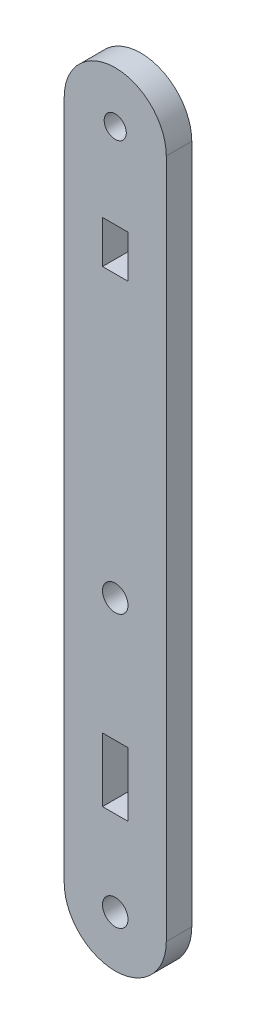
SolidWorks part; units mm, degrees
ref_plane "Front Plane" through (0, 0, 0) normal (0, 0, 1) x (1, 0, 0)
ref_plane "Top Plane" through (0, 0, 0) normal (0, 1, 0) x (1, 0, 0)
ref_plane "Right Plane" through (0, 0, 0) normal (1, 0, 0) x (0, 0, -1)
sketch "Model" plane through (0, 0, 0) normal (0, 0, 1) x (1, 0, 0)
  line L0 (36.3632, 82.8061) -> (36.3632, 2.8061)
  line L4 (48.3632, 82.8061) -> (48.3632, 2.806)
  line L6 (43.8632, 72.8061) -> (40.8632, 72.8061)
  line L7 (43.8632, 67.8061) -> (43.8632, 72.8061)
  line L8 (40.8632, 67.8061) -> (43.8632, 67.8061)
  line L9 (40.8632, 72.8061) -> (40.8632, 67.8061)
  line L10 (43.8632, 20.3061) -> (40.8632, 20.3061)
  line L11 (43.8632, 12.8061) -> (43.8632, 20.3061)
  line L12 (40.8632, 12.8061) -> (43.8632, 12.8061)
  line L13 (40.8632, 20.3061) -> (40.8632, 12.8061)
  circle A0 centre (42.3632, 34.806) radius 1.5
  circle A1 centre (42.3664, 2.813) radius 1.5
  circle A2 centre (42.3632, 82.8061) radius 1.3
  arc A3 (36.3632, 2.8061) -> (48.3632, 2.806) centre (42.3632, 2.806) ccw
  arc A4 (48.3632, 82.8061) -> (36.3632, 82.8061) centre (42.3632, 82.8061) ccw
extrude "Boss-Extrude1" add sketch "Model" along normal blind 3
